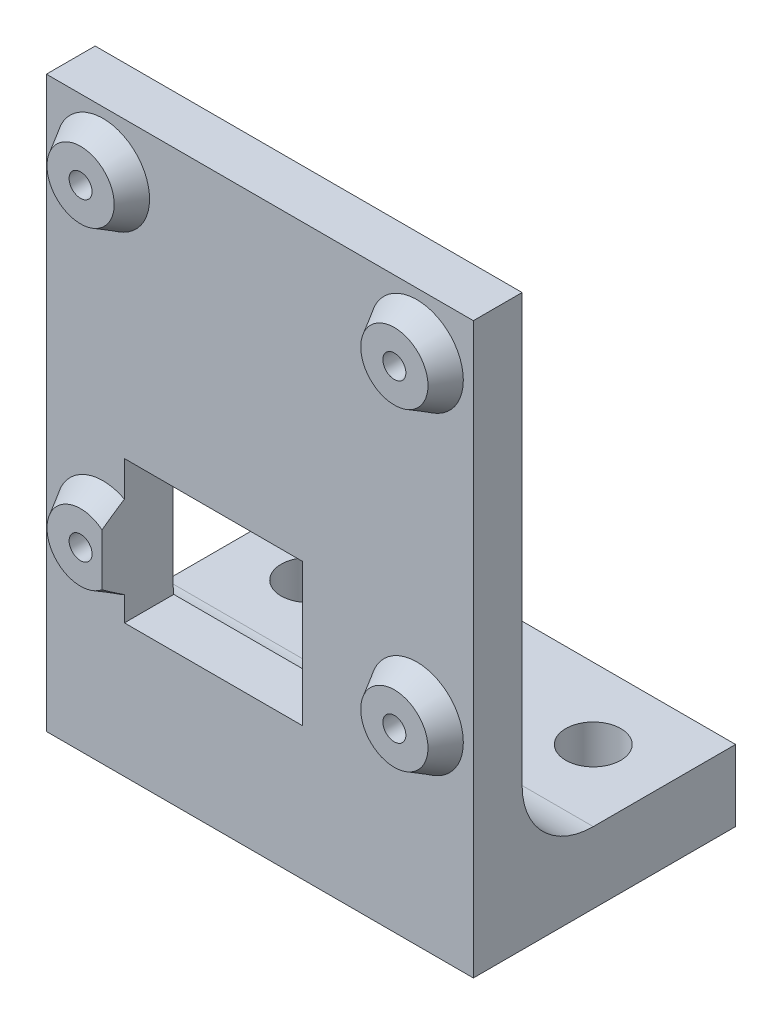
SolidWorks part; units mm, degrees
ref_plane "Front" through (0, 0, 0) normal (0, 0, 1) x (1, 0, 0)
ref_plane "Top" through (0, 0, 0) normal (0, 1, 0) x (1, 0, 0)
ref_plane "Right" through (0, 0, 0) normal (1, 0, 0) x (0, 0, -1)
sketch "Sketch1" plane through (0, 0, 0) normal (1, 0, 0) x (0, 0, -1)
  line L0 (25.4, 0) -> (0, 0)
  line L2 (0, 0) -> (0, 50.8)
  line L3 (0, 50.8) -> (6.35, 50.8)
  line L4 (6.35, 50.8) -> (6.35, 12.7)
  line L5 (12.7, 6.35) -> (25.4, 6.35)
  line L6 (25.4, 6.35) -> (25.4, 0)
  arc A0 (6.35, 12.7) -> (12.7, 6.35) centre (12.7, 12.7) ccw
  point P9 (53.682, 6.35)
  point P11 (-2.3256, 6.35)
  point P12 (0, 0.6968)
  dimension "D3" = 6.35
  dimension "D1" = 6.35
  dimension "D2" = 6.35
  dimension "D4" = 25.4
  dimension "D5" = 50.8
extrude "Boss-Extrude1" add sketch "Sketch1" along normal mid plane 38.1
sketch "Sketch4" plane through (0, 0, 0) normal (0, 0, 1) x (1, 0, 0)
  line L0 (-14, 45.75) -> (14, 17.75) construction
  line L3 (-14, 17.75) -> (14, 45.75) construction
  line L5 (-19.05, 50.8) -> (-14, 45.75) construction
  line L8 (14, 45.75) -> (19.05, 50.8) construction
  point P0 (-14, 45.75)
  point P2 (14, 45.75)
  point P4 (14, 17.75)
  point P6 (-14, 17.75)
  dimension "D1" = 28
hole_wizard "M2.5x0.45 Tapped Hole1" positions "Sketch4" profile "Sketch3" tap size "M2.5x0.45" standard "ANSI Metric" end condition through all
sketch "Sketch3" plane through (-14, 45.75, 0) normal (1, 0, 0) x (0, -1, 0)
  line L0 (0, 0) -> (0, 25.4)
  line L1 (0, 25.4) -> (1.025, 25.4)
  line L2 (1.025, 25.4) -> (1.025, 0)
  line L5 (1.025, 0) -> (0, 0)
  line L11 (0, -6.35) -> (0, 107.95) construction
  dimension "Thru Tap Drill Dia." = 2.05
  dimension "Thru Tap Drill Depth" = 25.4
cosmetic thread "Hole Thread1" parameters "D2"=2.5
cosmetic thread "Hole Thread2" parameters "D2"=2.5
cosmetic thread "Hole Thread3" parameters "D2"=2.5
cosmetic thread "Hole Thread4" parameters "D2"=2.5
sketch "Sketch6" plane through (0, 0, 0) normal (0, 0, 1) x (1, 0, 0)
  circle A0 centre (-14, 45.75) radius 3
  circle A1 centre (14, 45.75) radius 3
  circle A2 centre (14, 17.75) radius 3
  circle A3 centre (-14, 17.75) radius 3
  dimension "D1" = 6
extrude "Cut-Extrude1" cut sketch "Sketch6" against normal blind 2 draft 30 flip side to cut
sketch "Sketch7" plane through (0, 0, -2) normal (0, 0, 1) x (1, 0, 0)
  line L4 (-10.5, 20.1) -> (-12.0875, 24.575) construction
  line L5 (3.7875, 24.575) -> (-12.0875, 24.575)
  line L6 (3.7875, 24.575) -> (3.7875, 11.875)
  line L7 (3.7875, 11.875) -> (-12.0875, 11.875)
  line L12 (-10.5, 20.1) -> (-10.5, 16.35)
  line L13 (-3, 20.1) -> (-10.5, 20.1)
  line L14 (-3, 16.35) -> (-3, 20.1)
  line L15 (-10.5, 16.35) -> (-3, 16.35)
  line L16 (-10.5, 20.1) -> (-10.5, 16.35) construction
  line L17 (-3, 20.1) -> (-10.5, 20.1) construction
  line L18 (-3, 16.35) -> (-3, 20.1) construction
  line L19 (-10.5, 16.35) -> (-3, 16.35) construction
  line L20 (-12.0875, 24.575) -> (-12.0875, 11.875)
  line L21 (-10.5, 16.35) -> (-12.0875, 11.875) construction
  dimension "D2" = 12.7
  dimension "D3" = 15.875
  dimension "D4" = 1.5875
  dimension "D1" = 0
extrude "Cut-Extrude2" cut sketch "Sketch7" against normal through all both and the other way through all
sketch "Sketch10" plane through (0, 6.35, 0) normal (0, 1, 0) x (1, 0, 0)
  line L0 (-12.7, 19.05) -> (12.7, 19.05) construction
  line L2 (19.05, 25.4) -> (-19.05, 25.4) construction
  line L3 (-19.05, 25.4) -> (-12.7, 19.05) construction
  line L6 (12.7, 19.05) -> (19.05, 25.4) construction
  point P0 (-12.7, 19.05)
  point P2 (0, 19.05)
  point P4 (12.7, 19.05)
  dimension "D1" = 6.35
  dimension "D2" = 25.4
hole_wizard "#10 (0.1935) Diameter Hole1" positions "Sketch10" profile "Sketch9" hole size "#10" standard "ANSI Inch" end condition through all
sketch "Sketch9" plane through (-12.7, 6.35, -19.05) normal (1, 0, 0) x (0, 0, 1)
  line L0 (0, 0) -> (0, 6.35)
  line L1 (0, 6.35) -> (2.4574, 6.35)
  line L2 (2.4574, 6.35) -> (2.4574, 0)
  line L5 (2.4574, 0) -> (0, 0)
  line L11 (0, -6.35) -> (0, 107.95) construction
  dimension "Thru Hole Dia." = 4.9149
  dimension "Thru Hole Depth" = 6.35
